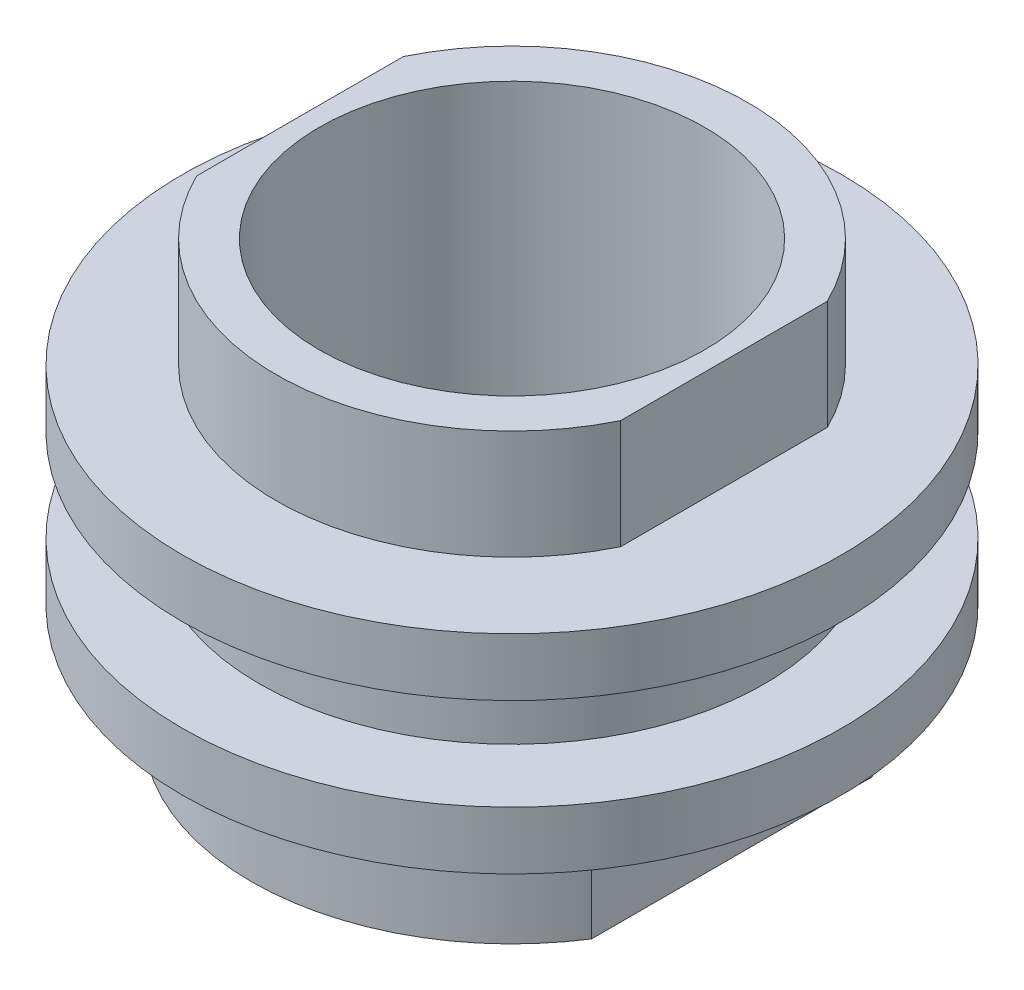
SolidWorks part; units mm, degrees
material "1060 Alloy"
ref_plane "Front Plane" through (0, 0, 0) normal (0, 0, 1) x (1, 0, 0)
ref_plane "Top Plane" through (0, 0, 0) normal (0, 1, 0) x (1, 0, 0)
ref_plane "Right Plane" through (0, 0, 0) normal (1, 0, 0) x (0, 0, -1)
sketch "Sketch1" plane through (0, 0, 0) normal (0, 1, 0) x (1, 0, 0)
  circle A0 centre (0, 0) radius 4.625
  dimension "D1" = 9.25
extrude "Boss-Extrude1" add sketch "Sketch1" along normal mid plane 1.69 contours A0
sketch "Sketch2" plane through (0, 0.845, 0) normal (0, 1, 0) x (1, 0, 0)
  circle A0 centre (0, 0) radius 6.035
  dimension "D1" = 12.07
extrude "Boss-Extrude2" add sketch "Sketch2" along normal blind 1.06 contours A0
sketch "Sketch3" plane through (0, -0.845, 0) normal (0, -1, 0) x (1, 0, 0)
  circle A0 centre (0, 0) radius 6.035
extrude "Boss-Extrude3" add sketch "Sketch3" along normal blind 1.06
sketch "Sketch4" plane through (0, 1.905, 0) normal (0, 1, 0) x (1, 0, 0)
  line L0 (-3.8813, 0) -> (-3.8813, 1.8922)
  line L1 (-3.8813, 1.8922) -> (-3.8813, -1.8922)
  line L2 (3.8813, 0) -> (3.8813, 1.8922)
  line L3 (3.8813, 1.8922) -> (3.8813, -1.8922)
  arc A0 (-3.8813, -1.8922) -> (3.8813, -1.8922) centre (0, 0) ccw
  arc A2 (3.8813, 1.8922) -> (-3.8813, 1.8922) centre (0, 0) ccw
  dimension "D1" = 8.636
extrude "Boss-Extrude4" add sketch "Sketch4" along normal blind 2 contours L2 A2 L0 L1 A0 L3
sketch "Sketch5" plane through (0, -1.905, 0) normal (0, -1, 0) x (1, 0, 0)
  line L0 (-4.0248, 0) -> (-4.0248, 2.5697)
  line L1 (-4.0248, 2.5697) -> (-4.0248, -2.5697)
  line L2 (4.0248, 0) -> (4.0248, 2.5697)
  line L3 (4.0248, 2.5697) -> (4.0248, -2.5697)
  arc A0 (-4.0248, -2.5697) -> (4.0248, -2.5697) centre (0, 0) ccw
  arc A2 (4.0248, 2.5697) -> (-4.0248, 2.5697) centre (0, 0) ccw
  dimension "D1" = 9.5504
extrude "Boss-Extrude5" add sketch "Sketch5" along normal blind 2 contours L2 A2 L0 L1 A0 L3
sketch "Sketch6" plane through (0, 3.905, 0) normal (0, 1, 0) x (1, 0, 0)
  circle A0 centre (0, 0) radius 3.5306
  dimension "D1" = 7.0612
extrude "Cut-Extrude1" cut sketch "Sketch6" against normal through all
